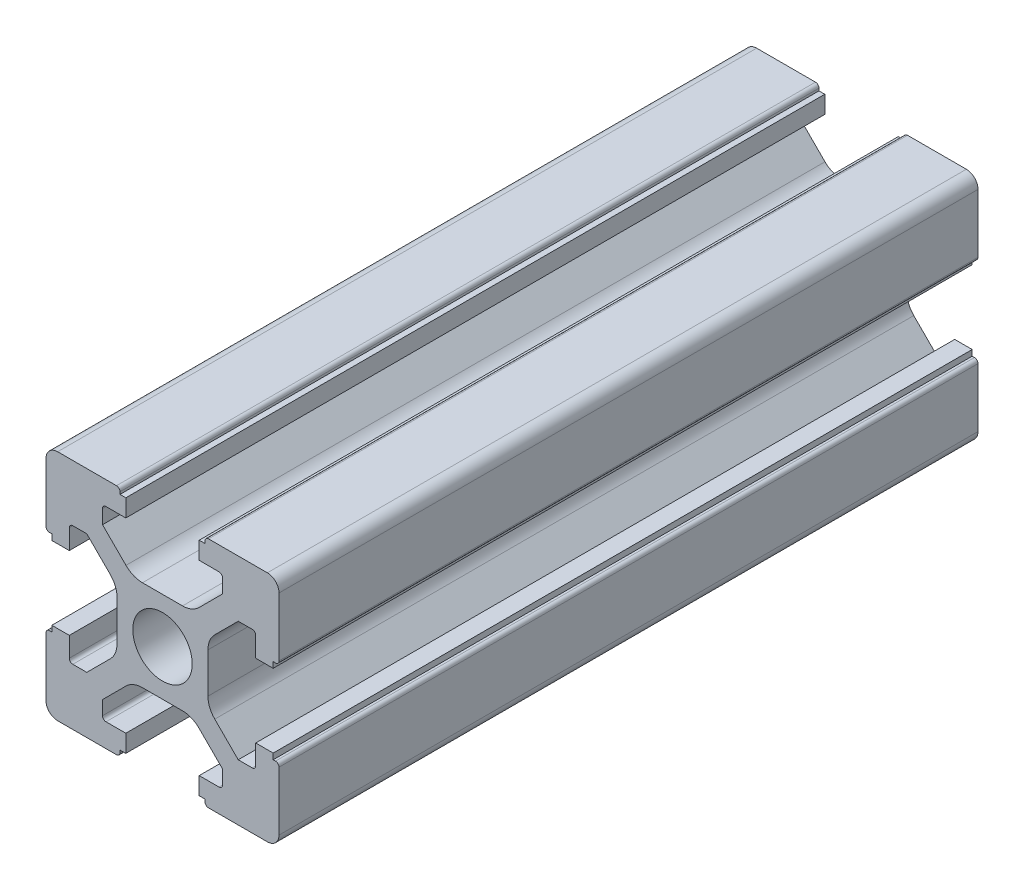
SolidWorks part; units mm, degrees
ref_plane "前视基准面" through (0, 0, 0) normal (0, 0, 1) x (1, 0, 0)
ref_plane "上视基准面" through (0, 0, 0) normal (0, 1, 0) x (1, 0, 0)
ref_plane "右视基准面" through (0, 0, 0) normal (1, 0, 0) x (0, 0, -1)
sketch "草图1" plane through (0, 0, 0) normal (0, 0, 1) x (1, 0, 0)
  line L1 (-10, -9) -> (-10, -3.95)
  line L3 (-9.7, -3.65) -> (-9.5, -3.65)
  line L5 (-9.5, -3.65) -> (-9.5, -3.15)
  line L7 (-9.5, -3.15) -> (-8, -3.15)
  line L9 (-8, -3.15) -> (-8, -4.85)
  line L11 (-7.7, -5.15) -> (-6.5, -5.15)
  line L13 (-6.5, -5.15) -> (-4.4858, -3.1358)
  line L15 (-3.9, -1.7216) -> (-3.9, 1.7216)
  line L17 (-6.5, 5.15) -> (-4.4858, 3.1358)
  line L19 (-7.7, 5.15) -> (-6.5, 5.15)
  line L21 (-8, 3.15) -> (-8, 4.85)
  line L23 (-9.5, 3.15) -> (-8, 3.15)
  line L25 (-9.5, 3.65) -> (-9.5, 3.15)
  line L27 (-9.7, 3.65) -> (-9.5, 3.65)
  line L29 (-10, 9) -> (-10, 3.95)
  line L31 (-9, 10) -> (-3.95, 10)
  line L33 (-3.65, 9.7) -> (-3.65, 9.5)
  line L35 (-3.65, 9.5) -> (-3.15, 9.5)
  line L37 (-3.15, 9.5) -> (-3.15, 8)
  line L39 (-3.15, 8) -> (-4.85, 8)
  line L41 (-5.15, 7.7) -> (-5.15, 6.5)
  line L43 (-5.15, 6.5) -> (-3.1358, 4.4858)
  line L45 (1.7216, 3.9) -> (-1.7216, 3.9)
  line L47 (5.15, 6.5) -> (3.1358, 4.4858)
  line L49 (5.15, 7.7) -> (5.15, 6.5)
  line L51 (3.15, 8) -> (4.85, 8)
  line L53 (3.15, 9.5) -> (3.15, 8)
  line L55 (3.65, 9.5) -> (3.15, 9.5)
  line L57 (3.65, 9.7) -> (3.65, 9.5)
  line L59 (9, 10) -> (3.95, 10)
  line L61 (10, 9) -> (10, 3.95)
  line L63 (9.7, 3.65) -> (9.5, 3.65)
  line L65 (9.5, 3.65) -> (9.5, 3.15)
  line L67 (9.5, 3.15) -> (8, 3.15)
  line L69 (8, 3.15) -> (8, 4.85)
  line L71 (7.7, 5.15) -> (6.5, 5.15)
  line L73 (6.5, 5.15) -> (4.4858, 3.1358)
  line L75 (3.9, 1.7216) -> (3.9, -1.7216)
  line L77 (6.5, -5.15) -> (4.4858, -3.1358)
  line L79 (7.7, -5.15) -> (6.5, -5.15)
  line L81 (8, -3.15) -> (8, -4.85)
  line L83 (9.5, -3.15) -> (8, -3.15)
  line L85 (9.5, -3.65) -> (9.5, -3.15)
  line L87 (9.7, -3.65) -> (9.5, -3.65)
  line L89 (10, -9) -> (10, -3.95)
  line L91 (9, -10) -> (3.95, -10)
  line L93 (3.65, -9.7) -> (3.65, -9.5)
  line L95 (3.65, -9.5) -> (3.15, -9.5)
  line L97 (3.15, -9.5) -> (3.15, -8)
  line L99 (3.15, -8) -> (4.85, -8)
  line L101 (5.15, -7.7) -> (5.15, -6.5)
  line L103 (5.15, -6.5) -> (3.1358, -4.4858)
  line L105 (-1.7216, -3.9) -> (1.7216, -3.9)
  line L107 (-5.15, -6.5) -> (-3.1358, -4.4858)
  line L109 (-5.15, -7.7) -> (-5.15, -6.5)
  line L111 (-3.15, -8) -> (-4.85, -8)
  line L113 (-3.15, -9.5) -> (-3.15, -8)
  line L115 (-3.65, -9.5) -> (-3.15, -9.5)
  line L117 (-3.65, -9.7) -> (-3.65, -9.5)
  line L119 (-9, -10) -> (-3.95, -10)
  ellipse E1 centre (0, 0) end of major axis (2.55, 0) minor radius 2.55
  ellipse E3 centre (-9, -9) end of major axis (-10, -9) minor radius 1 (-10, -9) -> (-9, -10) ccw
  ellipse E5 centre (-9.7, -3.95) end of major axis (-10, -3.95) minor radius 0.3 (-9.7, -3.65) -> (-10, -3.95) ccw
  ellipse E7 centre (-7.7, -4.85) end of major axis (-7.4, -4.85) minor radius 0.3 (-8, -4.85) -> (-7.7, -5.15) ccw
  ellipse E9 centre (-5.9, -1.7216) end of major axis (-5.9, -3.7216) minor radius 2 (-4.4858, -3.1358) -> (-3.9, -1.7216) ccw
  ellipse E11 centre (-5.9, 1.7216) end of major axis (-3.9, 1.7216) minor radius 2 (-3.9, 1.7216) -> (-4.4858, 3.1358) ccw
  ellipse E13 centre (-7.7, 4.85) end of major axis (-7.4, 4.85) minor radius 0.3 (-7.7, 5.15) -> (-8, 4.85) ccw
  ellipse E15 centre (-9.7, 3.95) end of major axis (-9.4, 3.95) minor radius 0.3 (-10, 3.95) -> (-9.7, 3.65) ccw
  ellipse E17 centre (-9, 9) end of major axis (-10, 9) minor radius 1 (-9, 10) -> (-10, 9) ccw
  ellipse E19 centre (-3.95, 9.7) end of major axis (-3.65, 9.7) minor radius 0.3 (-3.65, 9.7) -> (-3.95, 10) ccw
  ellipse E21 centre (-4.85, 7.7) end of major axis (-4.55, 7.7) minor radius 0.3 (-4.85, 8) -> (-5.15, 7.7) ccw
  ellipse E23 centre (-1.7216, 5.9) end of major axis (0.2784, 5.9) minor radius 2 (-3.1358, 4.4858) -> (-1.7216, 3.9) ccw
  ellipse E25 centre (1.7216, 5.9) end of major axis (-0.2784, 5.9) minor radius 2 (1.7216, 3.9) -> (3.1358, 4.4858) ccw
  ellipse E27 centre (4.85, 7.7) end of major axis (4.85, 8) minor radius 0.3 (5.15, 7.7) -> (4.85, 8) ccw
  ellipse E29 centre (3.95, 9.7) end of major axis (3.95, 10) minor radius 0.3 (3.95, 10) -> (3.65, 9.7) ccw
  ellipse E31 centre (9, 9) end of major axis (10, 9) minor radius 1 (10, 9) -> (9, 10) ccw
  ellipse E33 centre (9.7, 3.95) end of major axis (10, 3.95) minor radius 0.3 (9.7, 3.65) -> (10, 3.95) ccw
  ellipse E35 centre (7.7, 4.85) end of major axis (7.4, 4.85) minor radius 0.3 (8, 4.85) -> (7.7, 5.15) ccw
  ellipse E37 centre (5.9, 1.7216) end of major axis (7.9, 1.7216) minor radius 2 (4.4858, 3.1358) -> (3.9, 1.7216) ccw
  ellipse E39 centre (5.9, -1.7216) end of major axis (7.9, -1.7216) minor radius 2 (3.9, -1.7216) -> (4.4858, -3.1358) ccw
  ellipse E41 centre (7.7, -4.85) end of major axis (8, -4.85) minor radius 0.3 (7.7, -5.15) -> (8, -4.85) ccw
  ellipse E43 centre (9.7, -3.95) end of major axis (10, -3.95) minor radius 0.3 (10, -3.95) -> (9.7, -3.65) ccw
  ellipse E45 centre (9, -9) end of major axis (10, -9) minor radius 1 (9, -10) -> (10, -9) ccw
  ellipse E47 centre (3.95, -9.7) end of major axis (3.95, -9.4) minor radius 0.3 (3.65, -9.7) -> (3.95, -10) ccw
  ellipse E49 centre (4.85, -7.7) end of major axis (4.85, -7.4) minor radius 0.3 (4.85, -8) -> (5.15, -7.7) ccw
  ellipse E51 centre (1.7216, -5.9) end of major axis (1.7216, -3.9) minor radius 2 (3.1358, -4.4858) -> (1.7216, -3.9) ccw
  ellipse E53 centre (-1.7216, -5.9) end of major axis (-1.7216, -3.9) minor radius 2 (-1.7216, -3.9) -> (-3.1358, -4.4858) ccw
  ellipse E55 centre (-4.85, -7.7) end of major axis (-4.55, -7.7) minor radius 0.3 (-5.15, -7.7) -> (-4.85, -8) ccw
  ellipse E57 centre (-3.95, -9.7) end of major axis (-3.65, -9.7) minor radius 0.3 (-3.95, -10) -> (-3.65, -9.7) ccw
  dimension "D2" = 20
extrude "凸台-拉伸1" add sketch "草图1" along normal blind 60
